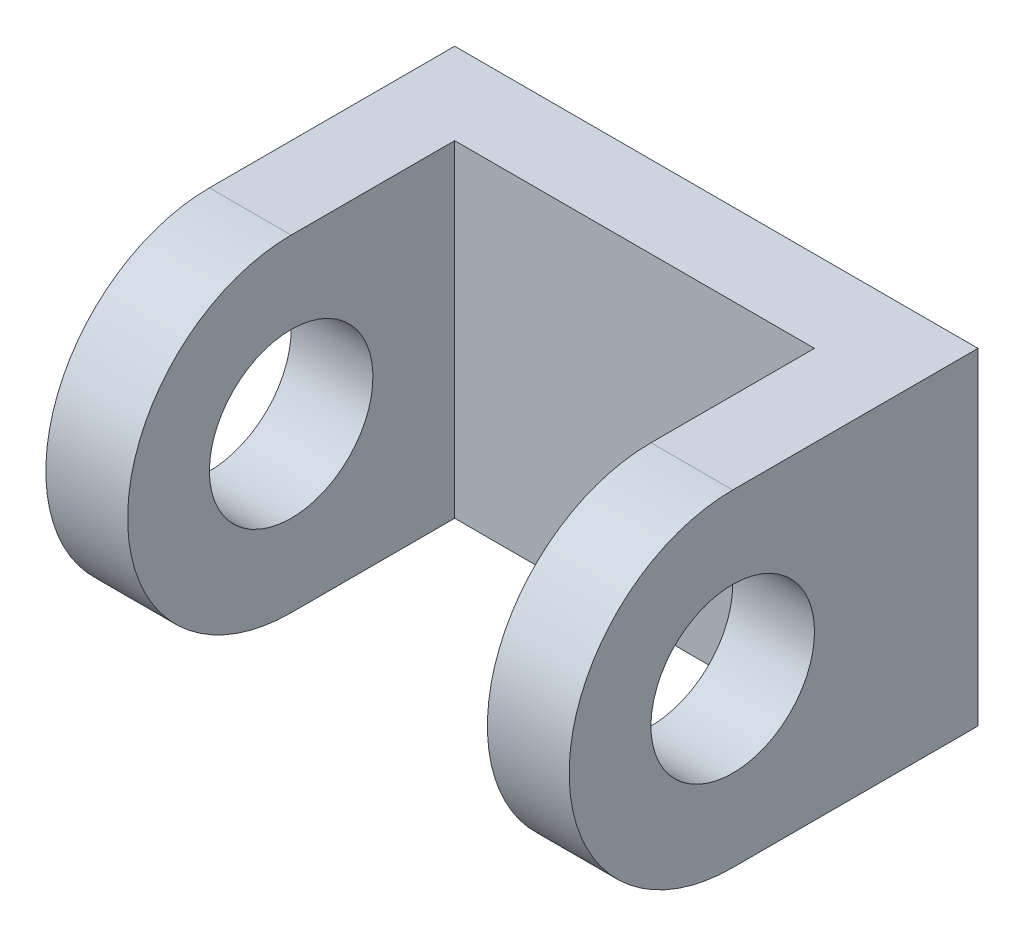
SolidWorks part; units mm, degrees
ref_plane "Front" through (0, 0, 0) normal (0, 0, 1) x (1, 0, 0)
ref_plane "Top" through (0, 0, 0) normal (0, 1, 0) x (1, 0, 0)
ref_plane "Right" through (0, 0, 0) normal (1, 0, 0) x (0, 0, -1)
sketch "Sketch1" plane through (0, 0, 0) normal (0, 0, 1) x (1, 0, 0)
  line L1 (-20.32, 12.7) -> (20.32, 12.7)
  line L2 (-20.32, 12.7) -> (-20.32, -12.7)
  line L3 (-20.32, -12.7) -> (20.32, -12.7)
  line L4 (20.32, 12.7) -> (20.32, -12.7)
  line L5 (-20.32, 12.7) -> (20.32, -12.7) construction
  line L6 (-20.32, -12.7) -> (20.32, 12.7) construction
  point P0 (0, 0)
  dimension "D1" = 40.64
  dimension "D2" = 25.4
extrude "Boss-Extrude1" add sketch "Sketch1" along normal blind 31.75
ref_plane "Plane1" through (-20.32, 12.7, 0) normal (0, 0, -1) x (-1, 0, 0)
sketch "Sketch3" plane through (0, 12.7, 0) normal (0, 1, 0) x (1, 0, 0)
  line L4 (-13.97, -31.75) -> (13.97, -31.75)
  line L5 (-13.97, -31.75) -> (-13.97, -6.35)
  line L6 (-13.97, -6.35) -> (20.32, -6.35)
  line L7 (-13.97, -31.75) -> (-13.97, -6.35)
  line L8 (-13.97, -6.35) -> (13.97, -6.35)
  line L9 (13.97, -31.75) -> (13.97, 0)
  line L10 (13.97, -31.75) -> (13.97, -6.35)
  dimension "D1" = 6.35
  dimension "D2" = 6.35
extrude "Cut-Extrude1" cut sketch "Sketch3" against normal through all
sketch "Sketch4" plane through (20.32, 0, 0) normal (1, 0, 0) x (0, 0, -1)
  line L0 (0, -12.7) -> (0, 12.7) construction
  circle A0 centre (-19.05, 0) radius 6.35
  dimension "D1" = 12.7
  dimension "D2" = 19.05
extrude "Cut-Extrude2" cut sketch "Sketch4" against normal through all
sketch "Sketch5" plane through (20.32, 0, 0) normal (1, 0, 0) x (0, 0, -1)
  line L0 (-31.75, 12.7) -> (0, 12.7) construction
  line L1 (-31.75, -12.7) -> (-31.75, 12.7) construction
  line L2 (-31.75, 12.7) -> (-19.05, 12.7)
  line L3 (-31.75, 0) -> (-31.75, 12.7)
  arc A0 (-19.05, 12.7) -> (-31.75, 0) centre (-19.05, 0) ccw
extrude "Cut-Extrude3" cut sketch "Sketch5" against normal through all
mirror "Mirror1" about plane through (0, 0, 0) normal (0, 1, 0) of "Cut-Extrude3"
